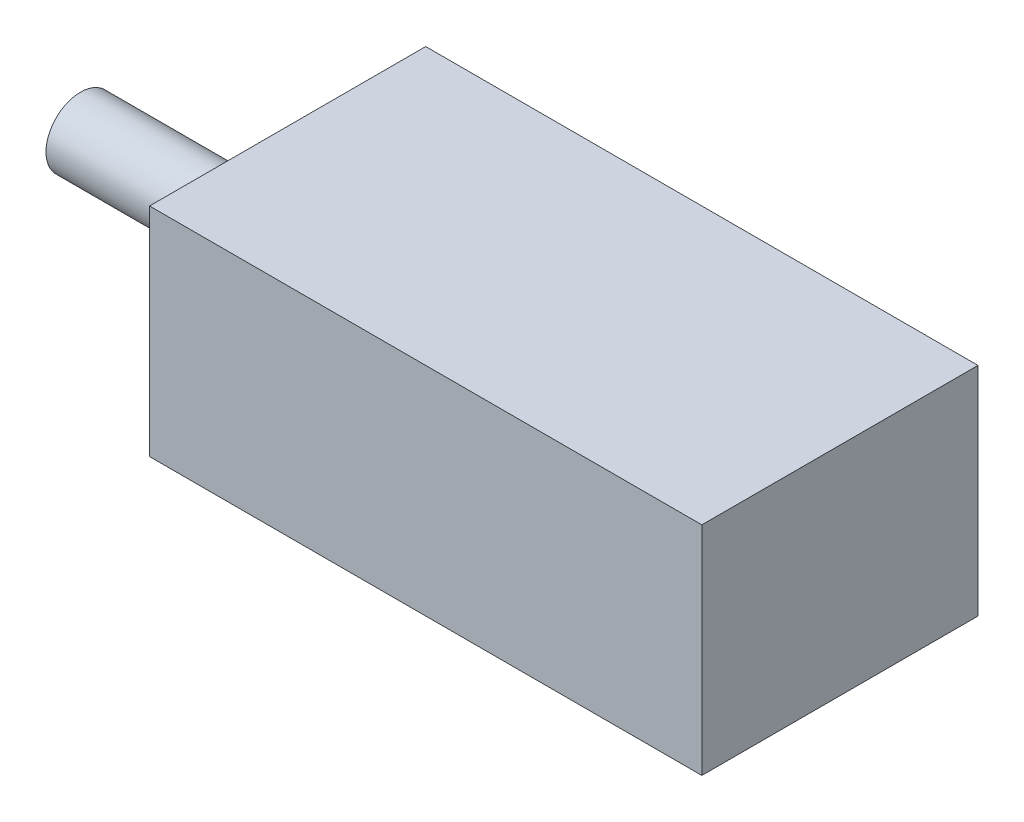
SolidWorks part; units mm, degrees
ref_plane "Front Plane" through (0, 0, 0) normal (0, 0, 1) x (1, 0, 0)
ref_plane "Top Plane" through (0, 0, 0) normal (0, 1, 0) x (1, 0, 0)
ref_plane "Right Plane" through (0, 0, 0) normal (1, 0, 0) x (0, 0, -1)
sketch "Sketch1" plane through (0, 0, 0) normal (0, 1, 0) x (1, 0, 0)
  line L1 (0, 0) -> (25.4, 0)
  line L2 (0, 0) -> (0, 12.7)
  line L3 (0, 12.7) -> (25.4, 12.7)
  line L4 (25.4, 0) -> (25.4, 12.7)
  dimension "D1" = 25.4
  dimension "D2" = 12.7
extrude "Boss-Extrude1" add sketch "Sketch1" along normal blind 9.9822
sketch "Sketch3" plane through (0, 0, 0) normal (-1, 0, 0) x (0, 0, 1)
  line L0 (-6.35, 9.9822) -> (-6.35, 0) construction
  line L1 (-12.7, 9.9822) -> (0, 9.9822) construction
  line L2 (-12.7, 0) -> (0, 0) construction
  line L3 (-12.7, 4.9911) -> (0, 4.9911) construction
  line L4 (-12.7, 9.9822) -> (-12.7, 0) construction
  line L5 (0, 9.9822) -> (0, 0) construction
  circle A0 centre (-6.35, 4.9911) radius 1.5875
  dimension "D1" = 3.175
extrude "Boss-Extrude2" add sketch "Sketch3" along normal blind 9.525
